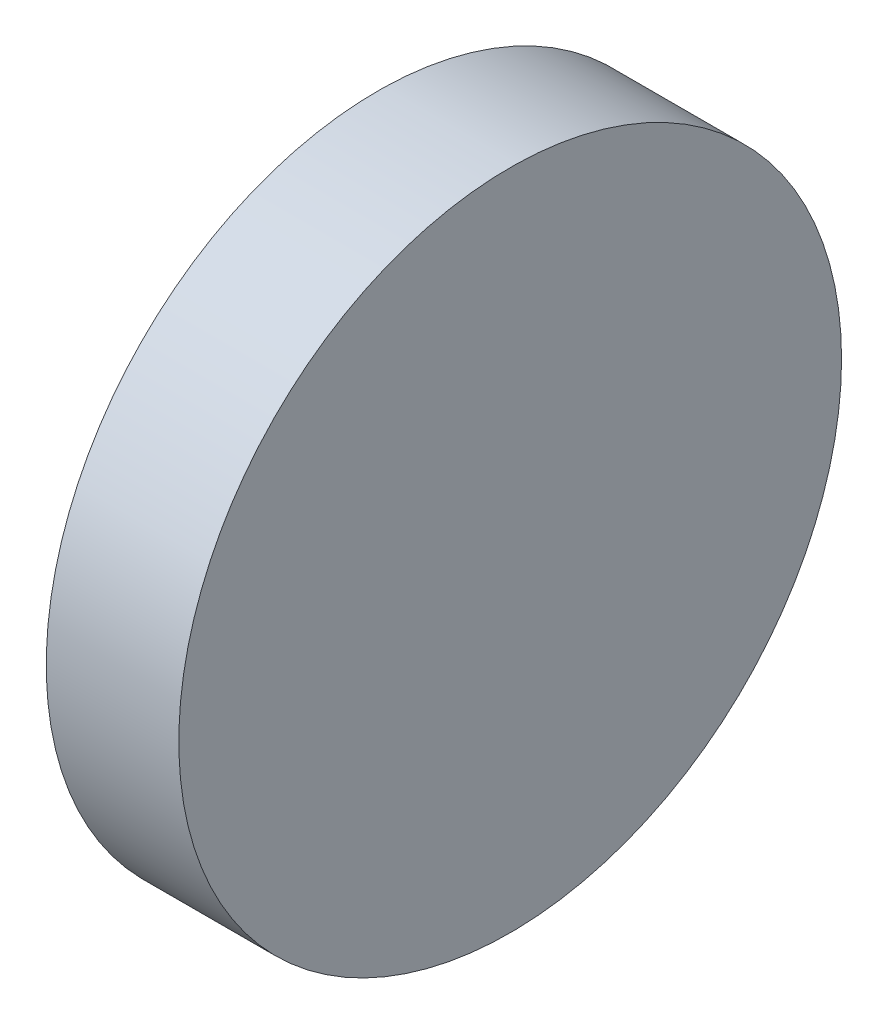
SolidWorks part; units mm, degrees
ref_plane "Front Plane" through (0, 0, 0) normal (0, 0, 1) x (1, 0, 0)
ref_plane "Top Plane" through (0, 0, 0) normal (0, 1, 0) x (1, 0, 0)
ref_plane "Right Plane" through (0, 0, 0) normal (1, 0, 0) x (0, 0, -1)
sketch "Sketch1" plane through (0, 0, 0) normal (1, 0, 0) x (0, 0, -1)
  circle A0 centre (0, 0) radius 31.75
extrude "Boss-Extrude1" add sketch "Sketch1" along normal blind 12.7
